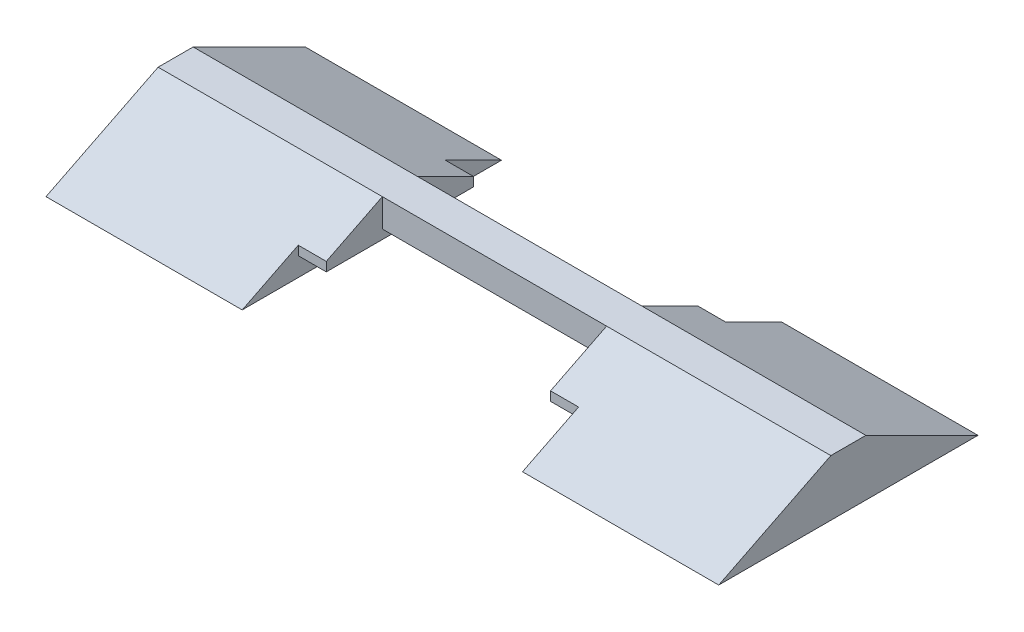
SolidWorks part; units mm, degrees
ref_plane "Front Plane" through (0, 0, 0) normal (0, 0, 1) x (1, 0, 0)
ref_plane "Top Plane" through (0, 0, 0) normal (0, 1, 0) x (1, 0, 0)
ref_plane "Right Plane" through (0, 0, 0) normal (1, 0, 0) x (0, 0, -1)
sketch "Sketch1" plane through (0, 0, 0) normal (0, 0, 1) x (1, 0, 0)
  line L10 (1, 0) -> (9, 0)
  line L12 (0, 1) -> (10, 1)
  line L14 (0, 1) -> (-7, 1)
  line L15 (0, -0.325) -> (0, -1)
  line L16 (0, -1) -> (-7, -1)
  line L17 (-7, 1) -> (-7, -1)
  line L18 (10, 1) -> (17, 1)
  line L19 (10, -0.325) -> (10, -1)
  line L20 (10, -1) -> (17, -1)
  line L21 (17, 1) -> (17, -1)
  line L24 (0, -0.325) -> (1, -0.325)
  line L25 (1, 0) -> (1, -0.325)
  line L28 (10, -0.325) -> (9, -0.325)
  line L29 (9, 0) -> (9, -0.325)
extrude "Boss-Extrude1" add sketch "Sketch1" along normal blind 1.25
sketch "Sketch2" plane through (0, 0, 1.25) normal (0, 0, 1) x (1, 0, 0)
  line L1 (1, -0.325) -> (0, -0.325)
  line L2 (1, -0.325) -> (1, 0)
  line L3 (1, 0) -> (0, 0)
  line L4 (0, -0.325) -> (0, 0)
  line L5 (9, -0.325) -> (10, -0.325)
  line L6 (9, -0.325) -> (9, 0)
  line L7 (9, 0) -> (10, 0)
  line L8 (10, -0.325) -> (10, 0)
  dimension "D1" = 0.325
  dimension "D2" = 1
extrude "Boss-Extrude2" add sketch "Sketch2" along normal blind 2
sketch "Sketch3" plane through (0, 0, 0) normal (0, 0, -1) x (-1, 0, 0)
  line L1 (-9, -0.325) -> (-10, -0.325)
  line L2 (-9, -0.325) -> (-9, 0)
  line L3 (-9, 0) -> (-10, 0)
  line L4 (-10, -0.325) -> (-10, 0)
  line L5 (-1, -0.325) -> (0, -0.325)
  line L6 (-1, -0.325) -> (-1, 0)
  line L7 (-1, 0) -> (0, 0)
  line L8 (0, -0.325) -> (0, 0)
  dimension "D1" = 1
  dimension "D2" = 0.325
  dimension "D3" = 1
  dimension "D4" = 0.325
extrude "Boss-Extrude3" add sketch "Sketch3" along normal blind 2
sketch "Sketch7" plane through (10, 0, 0) normal (1, 0, 0) x (0, 0, -1)
  line L0 (-3.25, 0) -> (-1.25, 1)
  line L1 (-1.25, 1) -> (-1.25, 0)
  line L2 (2, 0) -> (0, 1)
  line L3 (0, 1) -> (0, 0)
  line L4 (0, 0) -> (2, 0)
  line L6 (-1.25, -0.325) -> (-1.25, 0)
  line L7 (-1.25, 0) -> (-3.25, 0)
  line L8 (-3.25, 0) -> (-3.25, -0.325)
  line L9 (-3.25, -0.325) -> (-1.25, -0.325)
  line L10 (-1.25, -0.325) -> (-1.25, 0)
  line L12 (-3.25, 0) -> (-3.25, -0.325)
  line L13 (-3.25, -0.325) -> (-1.25, -0.325)
  dimension "D1" = 0
extrude "Boss-Extrude7" add sketch "Sketch7" against normal blind 1
sketch "Sketch8" plane through (0, 0, 0) normal (-1, 0, 0) x (0, 0, 1)
  line L0 (-2, 0) -> (0, 1)
  line L1 (0, 1) -> (0, 0)
  line L2 (0, 0) -> (-2, 0)
  line L3 (1.25, 1) -> (1.25, 0)
  line L4 (1.25, 0) -> (3.25, 0)
  line L5 (3.25, 0) -> (1.25, 1)
extrude "Boss-Extrude8" add sketch "Sketch8" against normal blind 1
sketch "Sketch10" plane through (0, 0, 0) normal (-1, 0, 0) x (0, 0, 1)
  line L0 (1.25, 1) -> (3.25, 0)
  line L1 (3.25, 0) -> (5.25, -1)
  line L2 (1.25, -1) -> (5.25, -1)
  line L3 (0, 1) -> (-2, 0)
  line L4 (-2, 0) -> (-4, -1)
  line L5 (0, -1) -> (-4, -1)
  line L6 (0, -1) -> (0, 1)
  line L7 (1.25, -1) -> (1.25, 1)
extrude "Boss-Extrude9" add sketch "Sketch10" along normal blind 7
sketch "Sketch11" plane through (10, 0, 0) normal (1, 0, 0) x (0, 0, -1)
  line L0 (-1.25, 1) -> (-5.25, -1)
  line L1 (-5.25, -1) -> (-1.25, -1)
  line L2 (-1.25, -1) -> (-1.25, 1)
  line L3 (0, 1) -> (4, -1)
  line L4 (4, -1) -> (0, -1)
  line L5 (0, -1) -> (0, 1)
extrude "Boss-Extrude10" add sketch "Sketch11" along normal blind 7
